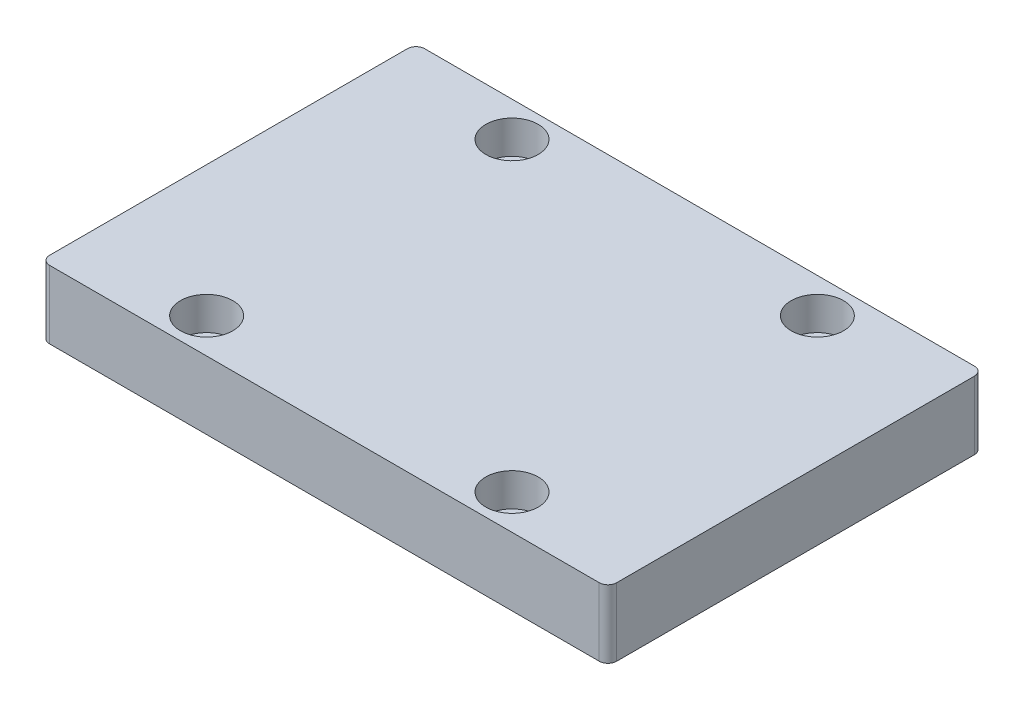
SolidWorks part; units mm, degrees
ref_plane "前视基准面" through (0, 0, 0) normal (0, 0, 1) x (1, 0, 0)
ref_plane "上视基准面" through (0, 0, 0) normal (0, 1, 0) x (1, 0, 0)
ref_plane "右视基准面" through (0, 0, 0) normal (1, 0, 0) x (0, 0, -1)
other "Configuration Table"
sketch "Sketch2" plane through (0, 0, 0) normal (0, 1, 0) x (1, 0, 0)
  line L1 (32.5, -21.5) -> (-32.5, -21.5)
  line L2 (32.5, -21.5) -> (32.5, 21.5)
  line L3 (32.5, 21.5) -> (-32.5, 21.5)
  line L4 (-32.5, -21.5) -> (-32.5, 21.5)
  line L5 (32.5, -21.5) -> (-32.5, 21.5) construction
  line L6 (32.5, 21.5) -> (-32.5, -21.5) construction
  point P0 (0, 0)
  dimension "D1" = 65
  dimension "D2" = 43
extrude "Boss-Extrude1" add sketch "Sketch2" along normal blind 7.8
fillet "Fillet1" radius 1 4 edges at (32.5, 3.9, -21.5) (-32.5, 3.9, -21.5) (-32.5, 3.9, 21.5) (32.5, 3.9, 21.5)
sketch "Sketch3" plane through (0, 7.8, 0) normal (0, 1, 0) x (1, 0, 0)
  line L0 (-17.5, 17.5) -> (17.5, 17.5) construction
  line L1 (17.5, -17.5) -> (-17.5, -17.5) construction
  line L2 (17.5, -17.5) -> (17.5, 17.5) construction
  line L3 (17.5, 17.5) -> (-17.5, 17.5) construction
  line L4 (-17.5, -17.5) -> (-17.5, 17.5) construction
  line L5 (17.5, -17.5) -> (-17.5, 17.5) construction
  line L6 (17.5, 17.5) -> (-17.5, -17.5) construction
  circle A0 centre (-17.5, 17.5) radius 1.6
  circle A1 centre (17.5, 17.5) radius 1.6
  circle A2 centre (17.5, -17.5) radius 1.6
  circle A3 centre (-17.5, -17.5) radius 1.6
  point P0 (0, 0)
  dimension "D2" = 3.2
  dimension "D1" = 35
  dimension "D5" = 35
  dimension "D3" = 2
  dimension "D4" = 2
extrude "Cut-Extrude1" cut sketch "Sketch3" against normal up to next
sketch "Sketch4" plane through (0, 7.8, 0) normal (0, 1, 0) x (1, 0, 0)
  circle A0 centre (-17.5, 17.5) radius 3
  circle A1 centre (17.5, 17.5) radius 3
  circle A2 centre (17.5, -17.5) radius 3
  circle A3 centre (-17.5, -17.5) radius 3
  dimension "D1" = 6
  dimension "D2" = 2
  dimension "D3" = 2
extrude "Cut-Extrude2" cut sketch "Sketch4" against normal blind 3.8
